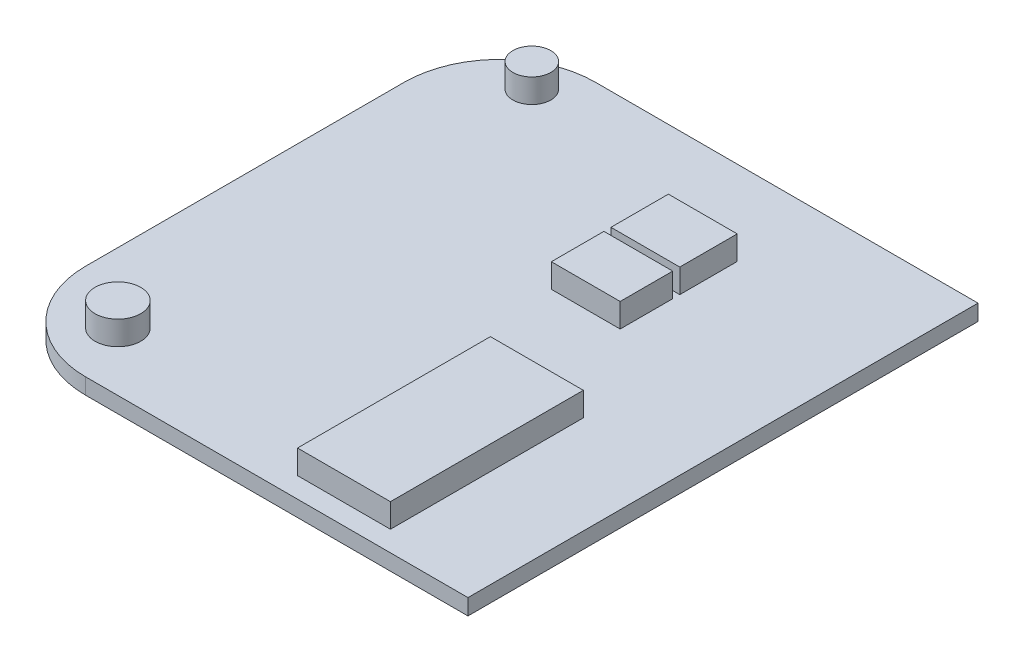
SolidWorks part; units mm, degrees
ref_plane "Front Plane" through (0, 0, 0) normal (0, 0, 1) x (1, 0, 0)
ref_plane "Top Plane" through (0, 0, 0) normal (0, 1, 0) x (1, 0, 0)
ref_plane "Right Plane" through (0, 0, 0) normal (1, 0, 0) x (0, 0, -1)
sketch "Sketch1" plane through (0, 0, 0) normal (0, 1, 0) x (1, 0, 0)
  line L1 (-6.9927, 15.2639) -> (17.0073, 15.2639)
  line L2 (-12.9927, 9.2639) -> (-12.9927, -10.7361)
  line L3 (-6.9927, -16.7361) -> (17.0073, -16.7361)
  line L4 (17.0073, 15.2639) -> (17.0073, -16.7361)
  arc A0 (-12.9927, -10.7361) -> (-6.9927, -16.7361) centre (-6.9927, -10.7361) ccw
  arc A1 (-6.9927, 15.2639) -> (-12.9927, 9.2639) centre (-6.9927, 9.2639) ccw
  point P8 (-12.9927, 15.2639)
  dimension "D3" = 6
  dimension "D1" = 32
  dimension "D2" = 30
extrude "Boss-Extrude1" add sketch "Sketch1" along normal blind 1
sketch "Sketch2" plane through (0, 1, 0) normal (0, 1, 0) x (1, 0, 0)
  line L1 (2.8741, 9.9724) -> (7.1915, 9.9724)
  line L2 (2.8741, 9.9724) -> (2.8741, 6.3689)
  line L3 (2.8741, 6.3689) -> (7.1915, 6.3689)
  line L4 (7.1915, 9.9724) -> (7.1915, 6.3689)
  line L5 (2.8741, 5.927) -> (7.1915, 5.927)
  line L6 (2.8741, 5.927) -> (2.8741, 2.6294)
  line L7 (2.8741, 2.6294) -> (7.1915, 2.6294)
  line L8 (7.1915, 5.927) -> (7.1915, 2.6294)
  line L9 (5.0328, -3.3537) -> (10.863, -3.3537)
  line L10 (5.0328, -3.3537) -> (5.0328, -15.4559)
  line L11 (5.0328, -15.4559) -> (10.863, -15.4559)
  line L12 (10.863, -3.3537) -> (10.863, -15.4559)
extrude "Boss-Extrude2" add sketch "Sketch2" along normal blind 1.5
sketch "Sketch3" plane through (0, 1, 0) normal (0, 1, 0) x (1, 0, 0)
  circle A0 centre (-8.6162, -13.0763) radius 1.433
  circle A1 centre (-8.6162, 12.8959) radius 1.1898
extrude "Boss-Extrude3" add sketch "Sketch3" along normal blind 1.5
